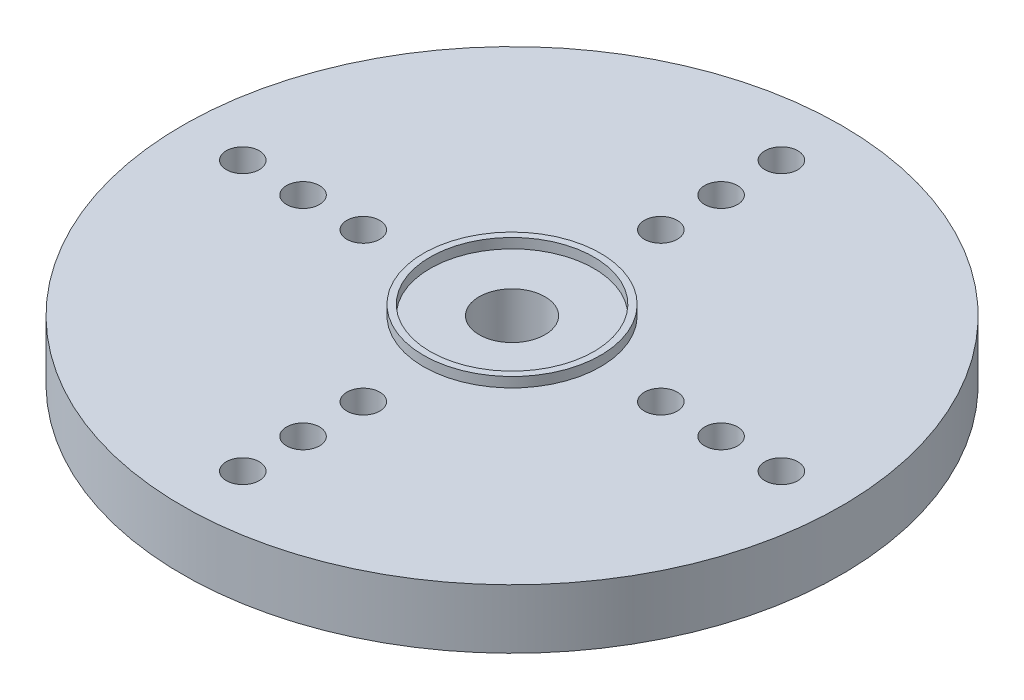
SolidWorks part; units mm, degrees
ref_plane "Front Plane" through (0, 0, 0) normal (0, 0, 1) x (1, 0, 0)
ref_plane "Top Plane" through (0, 0, 0) normal (0, 1, 0) x (1, 0, 0)
ref_plane "Right Plane" through (0, 0, 0) normal (1, 0, 0) x (0, 0, -1)
sketch "Sketch1" plane through (0, 0, 0) normal (0, 0, 1) x (1, 0, 0)
  line L0 (1, 2.26) -> (1, 4.06)
  line L1 (1, 4.06) -> (10, 4.06)
  line L2 (10, 4.06) -> (10, 2.26)
  line L3 (10, 2.26) -> (3.5, 2.26)
  line L4 (3.5, 2.26) -> (3.5, 0)
  line L5 (3.5, 0) -> (2.435, 0)
  line L6 (0, 0) -> (0, 4.06) construction
  line L7 (1, 2.26) -> (2.435, 2.26)
  line L8 (2.435, 2.26) -> (2.435, 0)
  dimension "D1" = 1
  dimension "D2" = 10
  dimension "D3" = 3.5
  dimension "D4" = 2.26
  dimension "D5" = 1.8
  dimension "D6" = 2.435
revolve "Revolve2" add sketch "Sketch1" angle 360 about L6
sketch "Sketch2" plane through (0, 4.06, 0) normal (0, 1, 0) x (1, 0, 0)
  circle A0 centre (0, 0) radius 2.685
  circle A1 centre (0, 0) radius 2.485
  dimension "D1" = 5.37
  dimension "D2" = 4.97
extrude "Boss-Extrude1" add sketch "Sketch2" along normal blind 0.3
sketch "Sketch4" plane through (0, 0, 0) normal (0, 1, 0) x (1, 0, 0)
  line L0 (0, 2.685) -> (0, 4.5138) construction
  line L1 (0, 4.5138) -> (0, 6.3425) construction
  line L2 (0, 6.3425) -> (0, 8.1713) construction
  line L3 (0, 8.1713) -> (0, 10) construction
  circle A0 centre (0, 4.5138) radius 0.5
  circle A1 centre (0, 6.3425) radius 0.5
  circle A2 centre (0, 8.1713) radius 0.5
  circle A5 centre (0, 0) radius 2.685 construction
  circle A6 centre (0, 0) radius 10 construction
  dimension "D1" = 1
extrude "Cut-Extrude2" cut sketch "Sketch4" along normal through all
pattern_circular "CirPattern1" count 4 every 90 about axis through (0, 0, 0) along (0, 1, 0) of "Cut-Extrude2"
